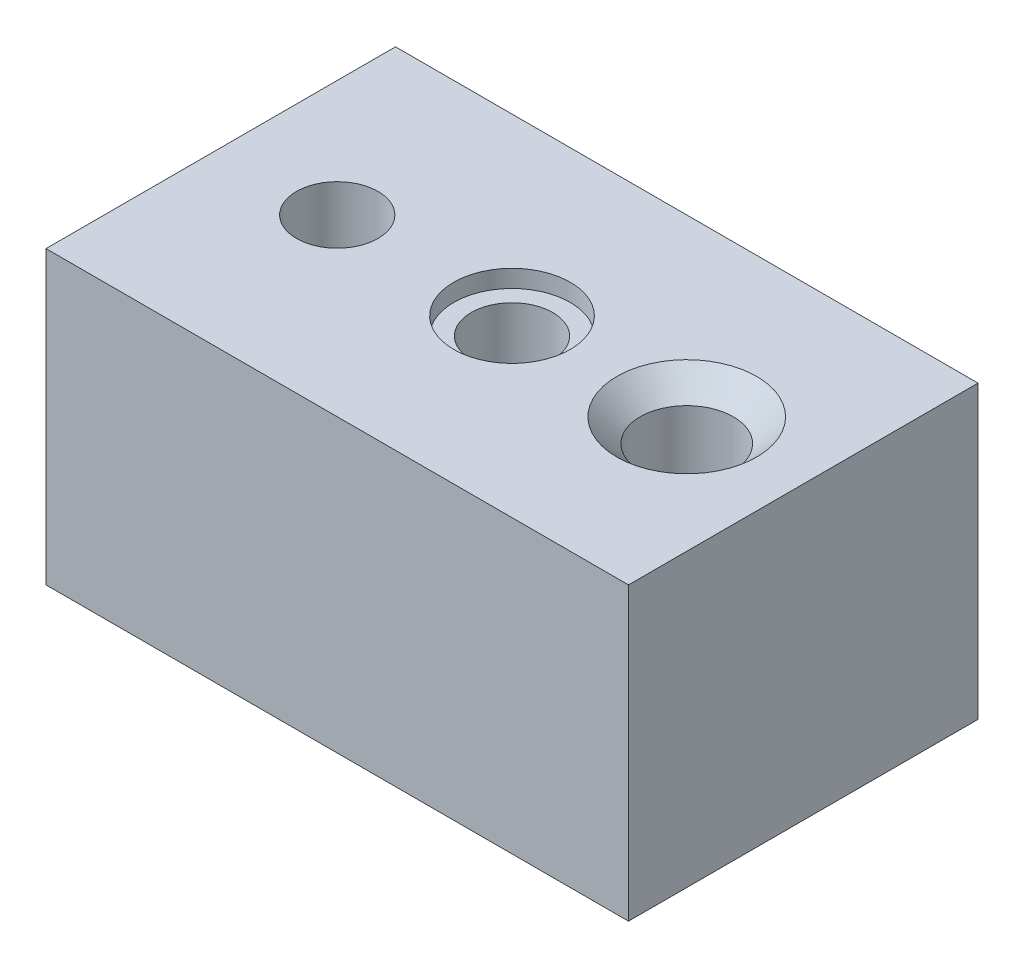
SolidWorks part; units mm, degrees
ref_plane "Front Plane" through (0, 0, 0) normal (0, 0, 1) x (1, 0, 0)
ref_plane "Top Plane" through (0, 0, 0) normal (0, 1, 0) x (1, 0, 0)
ref_plane "Right Plane" through (0, 0, 0) normal (1, 0, 0) x (0, 0, -1)
sketch "Sketch1" plane through (0, 0, 0) normal (0, 1, 0) x (1, 0, 0)
  line L1 (0, 0) -> (100, 0)
  line L2 (0, 0) -> (0, 60)
  line L3 (0, 60) -> (100, 60)
  line L4 (100, 0) -> (100, 60)
  dimension "D1" = 100
  dimension "D2" = 60
extrude "Boss-Extrude2" add sketch "Sketch1" along normal blind 50
hole_wizard "CBORE for M5 Hex Head Bolt1" positions "Sketch17" profile "Sketch18" counterbore size "M5" standard "ANSI Metric"
sketch "Sketch17" plane through (0, 50, 0) normal (0, 1, 0) x (1, 0, 0)
  line L0 (0, 60) -> (0, 0) construction
  line L1 (0, 0) -> (100, 0) construction
  point P0 (50, 30)
  dimension "D1" = 50
  dimension "D2" = 30
sketch "Sketch18" plane through (50, 50, -30) normal (1, 0, 0) x (0, 0, 1)
  line L0 (0, 0) -> (0, 20.206)
  line L1 (0, 20.206) -> (7, 16)
  line L2 (7, 16) -> (7, 3)
  line L3 (7, 3) -> (10, 3)
  line L4 (10, 3) -> (10, 0)
  line L5 (10, 0) -> (0, 0)
  line L10 (0, 20.206) -> (-7, 16) construction
  line L11 (0, -6.35) -> (0, 107.95) construction
  dimension "Hole Dia." = 14
  dimension "Hole Depth" = 16
  dimension "C'Bore Dia." = 20
  dimension "C'Bore Depth" = 3
  dimension "Drill Angle" = 118
hole_wizard "CSK for M5 Flat Head Machine Screw1" positions "Sketch19" profile "Sketch20" countersink size "M5" standard "ANSI Metric"
sketch "Sketch19" plane through (0, 50, 0) normal (0, 1, 0) x (1, 0, 0)
  line L0 (0, 60) -> (0, 0) construction
  line L1 (0, 0) -> (100, 0) construction
  point P0 (80, 30)
  dimension "D1" = 80
  dimension "D2" = 30
sketch "Sketch20" plane through (80, 50, -30) normal (1, 0, 0) x (0, 0, 1)
  line L0 (0, 0) -> (0, 20.8069)
  line L1 (0, 20.8069) -> (8, 16)
  line L2 (8, 16) -> (8, 4)
  line L3 (8, 4) -> (12, 0)
  line L5 (12, 0) -> (0, 0)
  line L6 (-8, 4) -> (-12, 0) construction
  line L10 (0, 20.8069) -> (-8, 16) construction
  line L11 (0, -6.35) -> (0, 107.95) construction
  dimension "Hole Dia." = 16
  dimension "Hole Depth" = 16
  dimension "Near C'Sink Dia." = 24
  dimension "Near C'Sink Angle" = 90
  dimension "Drill Angle" = 118
hole_wizard "M16x2.0 Tapped Hole1" positions "Sketch21" profile "Sketch22" tap size "M16x2.0" standard "ANSI Metric" end condition through all
sketch "Sketch21" plane through (0, 50, 0) normal (0, 1, 0) x (1, 0, 0)
  line L0 (0, 0) -> (100, 0) construction
  line L1 (0, 60) -> (0, 0) construction
  point P0 (20, 30)
  dimension "D1" = 30
  dimension "D2" = 20
sketch "Sketch22" plane through (20, 50, -30) normal (1, 0, 0) x (0, 0, 1)
  line L0 (0, 0) -> (0, 50)
  line L1 (0, 50) -> (7, 50)
  line L2 (7, 50) -> (7, 0)
  line L5 (7, 0) -> (0, 0)
  line L11 (0, -6.35) -> (0, 107.95) construction
  dimension "Thru Tap Drill Dia." = 14
  dimension "Thru Tap Drill Depth" = 50
cosmetic thread "Hole Thread1" parameters "D2"=16
